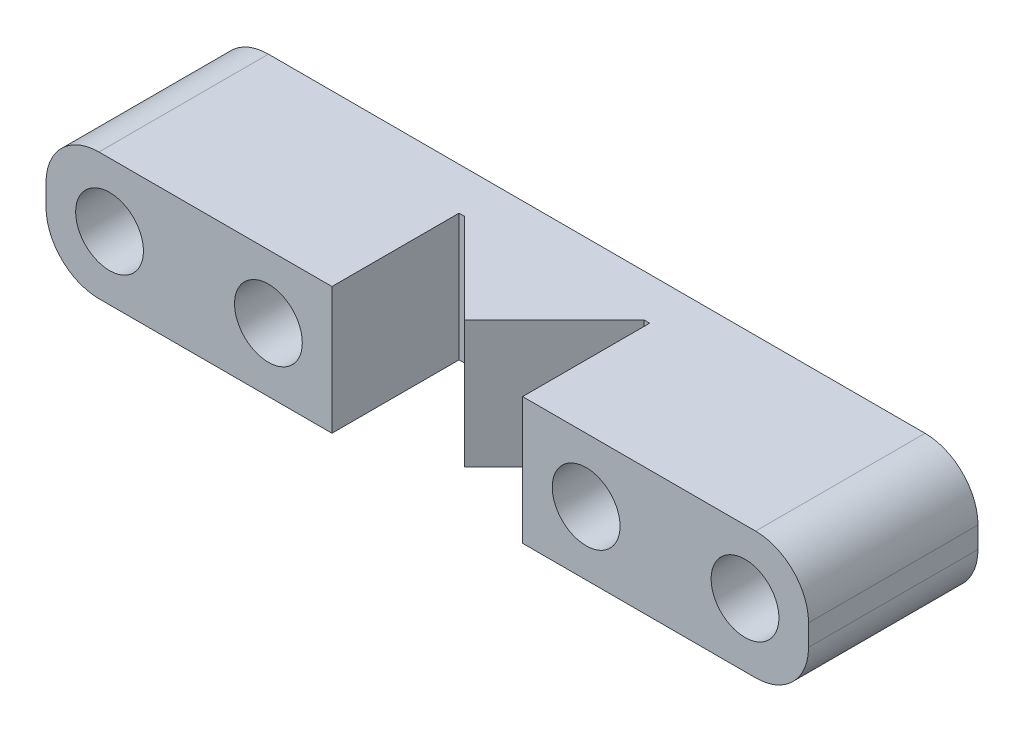
SolidWorks part; units mm, degrees
ref_plane "Front Plane" through (0, 0, 0) normal (0, 0, 1) x (1, 0, 0)
ref_plane "Top Plane" through (0, 0, 0) normal (0, 1, 0) x (1, 0, 0)
ref_plane "Right Plane" through (0, 0, 0) normal (1, 0, 0) x (0, 0, -1)
sketch "Sketch1" plane through (0, 0, 0) normal (0, 0, 1) x (1, 0, 0)
  line L1 (-0.5, 3) -> (15.5, 3)
  line L2 (-3, 0.5) -> (-3, -0.5)
  line L3 (-0.5, -3) -> (15.5, -3)
  line L4 (18, 0.5) -> (18, -0.5)
  circle A0 centre (0, 0) radius 1.6
  circle A1 centre (15, 0) radius 1.6
  arc A2 (15.5, -3) -> (18, -0.5) centre (15.5, -0.5) ccw
  arc A3 (15.5, 3) -> (18, 0.5) centre (15.5, 0.5) cw
  arc A4 (-3, -0.5) -> (-0.5, -3) centre (-0.5, -0.5) ccw
  arc A5 (-0.5, 3) -> (-3, 0.5) centre (-0.5, 0.5) ccw
  point P13 (18, 3)
  point P18 (-3, 3)
  dimension "D1" = 3.2
  dimension "D5" = 3.2
  dimension "D6" = 3
  dimension "D9" = 2.5
  dimension "D2" = 3
  dimension "D3" = 3
  dimension "D4" = 3
  dimension "D7" = 3
  dimension "D8" = 21
extrude "Boss-Extrude1" add sketch "Sketch1" along normal blind 8
sketch "Sketch2" plane through (0, -3, 0) normal (0, -1, 0) x (1, 0, 0)
  line L0 (18, 8) -> (18, 0) construction
  line L1 (3, 10.1997) -> (12, 10.1997)
  line L2 (3, 10.1997) -> (3, 2)
  line L3 (3, 2) -> (12, 2)
  line L4 (12, 10.1997) -> (12, 2)
  line L5 (-3, 8) -> (-3, 0) construction
  line L6 (-0.5, 0) -> (15.5, 0) construction
  dimension "D1" = 6
  dimension "D2" = 6
  dimension "D3" = 2
extrude "Cut-Extrude1" cut sketch "Sketch2" against normal blind 8
sketch "Sketch3" plane through (0, -3, 0) normal (0, -1, 0) x (1, 0, 0)
  line L0 (3.2574, 2) -> (7.5, 6.2426)
  line L1 (3, 2) -> (12, 2) construction
  line L2 (7.5, 6.2426) -> (11.7426, 2)
  line L3 (11.7426, 2) -> (3.2574, 2)
  line L5 (-0.5, 0) -> (15.5, 0) construction
  point P4 (10.1425, 7.1892)
  point P6 (8.9245, 7.818)
  point P7 (0, 0)
  point P10 (7.5, 0)
  point P11 (9, 6.874)
  dimension "D1" = 90
  dimension "D2" = 45
  dimension "D3" = 6
extrude "Boss-Extrude2" add sketch "Sketch3" against normal up to surface (6 mm away) up to face at (7.5, 3, 4.5)
sketch "Sketch4" plane through (0, 0, 0) normal (0, 0, -1) x (-1, 0, 0)
  line L0 (-3, 3) -> (0.5, 3) construction
  line L1 (0.5, 3) -> (8, 3)
  line L3 (0.5, -3) -> (8, -3)
  line L4 (10.5, 0.5) -> (10.5, -0.5)
  line L5 (-7.5, 3) -> (-7.5, 9.1942) construction
  line L6 (-25.5, 0.5) -> (-25.5, -0.5)
  line L7 (-15.5, -3) -> (-23, -3)
  line L8 (-15.5, 3) -> (-23, 3)
  arc A0 (3, 0.5) -> (0.5, 3) centre (0.5, 0.5) ccw construction
  circle A1 centre (7.5, 0) radius 1.6
  arc A2 (8, -3) -> (10.5, -0.5) centre (8, -0.5) ccw
  arc A3 (8, 3) -> (10.5, 0.5) centre (8, 0.5) cw
  arc A4 (-23, 3) -> (-25.5, 0.5) centre (-23, 0.5) ccw
  arc A5 (-23, -3) -> (-25.5, -0.5) centre (-23, -0.5) cw
  circle A6 centre (-22.5, 0) radius 1.6
  arc M4 (-18, -0.5) -> (-15.5, -3) centre (-15.5, -0.5) ccw
  arc M6 (0.5, -3) -> (3, -0.5) centre (0.5, -0.5) ccw
  line M7 (3, -0.5) -> (3, 0.5)
  arc M8 (3, 0.5) -> (0.5, 3) centre (0.5, 0.5) ccw
  arc M10 (-15.5, 3) -> (-18, 0.5) centre (-15.5, 0.5) ccw
  line M11 (-18, 0.5) -> (-18, -0.5)
  dimension "D1" = 3.2
  dimension "D3" = 2.5
  dimension "D2" = 7.5
  dimension "D4" = 3
extrude "Boss-Extrude3" add sketch "Sketch4" against normal blind 8 contours A3 L1 L3 A2 L4 A1 M8 M7 M6 | A5 L7 L8 A4 L6 A6 M4 M11 M10
